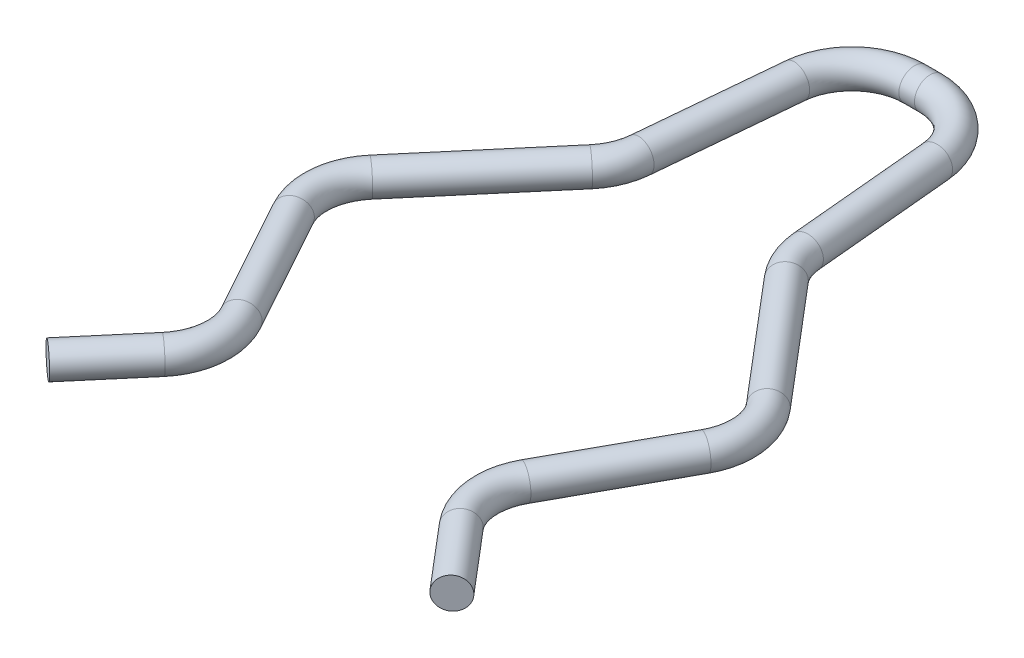
SolidWorks part; units mm, degrees
material "A286 Iron Base Superalloy"
ref_plane "Front Plane" through (0, 0, 0) normal (0, 0, 1) x (1, 0, 0)
ref_plane "Top Plane" through (0, 0, 0) normal (0, 1, 0) x (1, 0, 0)
ref_plane "Right Plane" through (0, 0, 0) normal (1, 0, 0) x (0, 0, -1)
sketch "Sketch1" plane through (0, 0, 0) normal (0, 1, 0) x (1, 0, 0)
  line L0 (-6.3589, 1.7809) -> (-3.1297, 5.5842)
  line L1 (-2.6627, 6.6945) -> (-2.2415, 11.2498)
  line L2 (-6.5863, -0.4784) -> (-4.54, -4.194)
  line L3 (-4.7673, -6.4533) -> (-6.4637, -8.4511)
  line L4 (0, 15.8956) -> (0, -11.3761) construction
  line L5 (4.7673, -6.4533) -> (6.4637, -8.4511)
  line L6 (6.5863, -0.4784) -> (4.54, -4.194)
  line L7 (6.3589, 1.7809) -> (3.1297, 5.5842)
  line L8 (2.6627, 6.6945) -> (2.2415, 11.2498)
  line L9 (-0.25, 13.0656) -> (0.25, 13.0656)
  circle A0 centre (0, 0) radius 6 construction
  arc A1 (3.1297, 5.5842) -> (2.6627, 6.6945) centre (4.6542, 6.8787) cw
  arc A2 (6.5863, -0.4784) -> (6.3589, 1.7809) centre (4.8344, 0.4864) ccw
  arc A3 (4.7673, -6.4533) -> (4.54, -4.194) centre (6.2919, -5.1588) cw
  arc A4 (-4.54, -4.194) -> (-4.7673, -6.4533) centre (-6.2919, -5.1588) cw
  arc A5 (-6.3589, 1.7809) -> (-6.5863, -0.4784) centre (-4.8344, 0.4864) ccw
  arc A6 (-3.1297, 5.5842) -> (-2.6627, 6.6945) centre (-4.6542, 6.8787) ccw
  arc A7 (2.2415, 11.2498) -> (0.25, 13.0656) centre (0.25, 11.0656) ccw
  arc A8 (-2.2415, 11.2498) -> (-0.25, 13.0656) centre (-0.25, 11.0656) cw
  point P14 (0, 13.0656)
  point P18 (2.7209, 6.0656)
  point P21 (7.2516, 0.7296)
  point P24 (3.8747, -5.402)
  point P27 (-3.8747, -5.402)
  point P30 (-7.2516, 0.7296)
  point P33 (-2.7209, 6.0656)
  point P36 (2.0736, 13.0656)
  point P39 (-2.0736, 13.0656)
  dimension "D1" = 12
  dimension "D7" = 2
  dimension "D8" = 4.7673
  dimension "D2" = 7
  dimension "D3" = 4
  dimension "D4" = 7
  dimension "D5" = 7
  dimension "D6" = 0.5
  dimension "D9" = 4.54
sweep "Sweep2" add path "Sketch1" circular profile diameter 1 parameters "D3"=1
